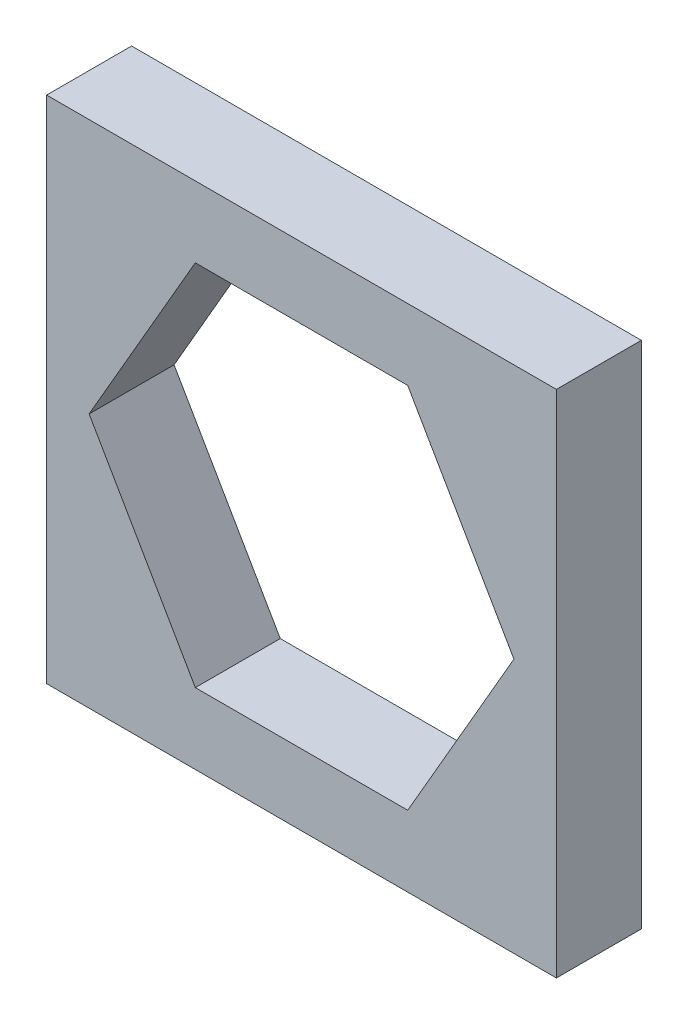
SolidWorks part; units mm, degrees
ref_plane "Piano frontale" through (0, 0, 0) normal (0, 0, 1) x (1, 0, 0)
ref_plane "Piano superiore" through (0, 0, 0) normal (0, 1, 0) x (1, 0, 0)
ref_plane "Piano destro" through (0, 0, 0) normal (1, 0, 0) x (0, 0, -1)
sketch "Schizzo1" plane through (0, 0, 0) normal (0, 0, 1) x (1, 0, 0)
  line L0 (12.5, -21.6506) -> (25, 0)
  line L1 (-30, 30) -> (30, 30)
  line L2 (-30, 30) -> (-30, -30)
  line L3 (-30, -30) -> (30, -30)
  line L4 (30, 30) -> (30, -30)
  line L5 (25, 0) -> (12.5, 21.6506)
  line L6 (12.5, 21.6506) -> (-12.5, 21.6506)
  line L7 (-12.5, 21.6506) -> (-25, 0)
  line L8 (-25, 0) -> (-12.5, -21.6506)
  line L9 (-12.5, -21.6506) -> (12.5, -21.6506)
  circle A0 centre (0, 0) radius 25 construction
  dimension "D1" = 60
  dimension "D2" = 60
  dimension "D3" = 30
extrude "Estrusione-Estrusione1" add sketch "Schizzo1" along normal blind 10 contours L5 L6 L7 L8 L9 L0 | L1 L4 L3 L2
